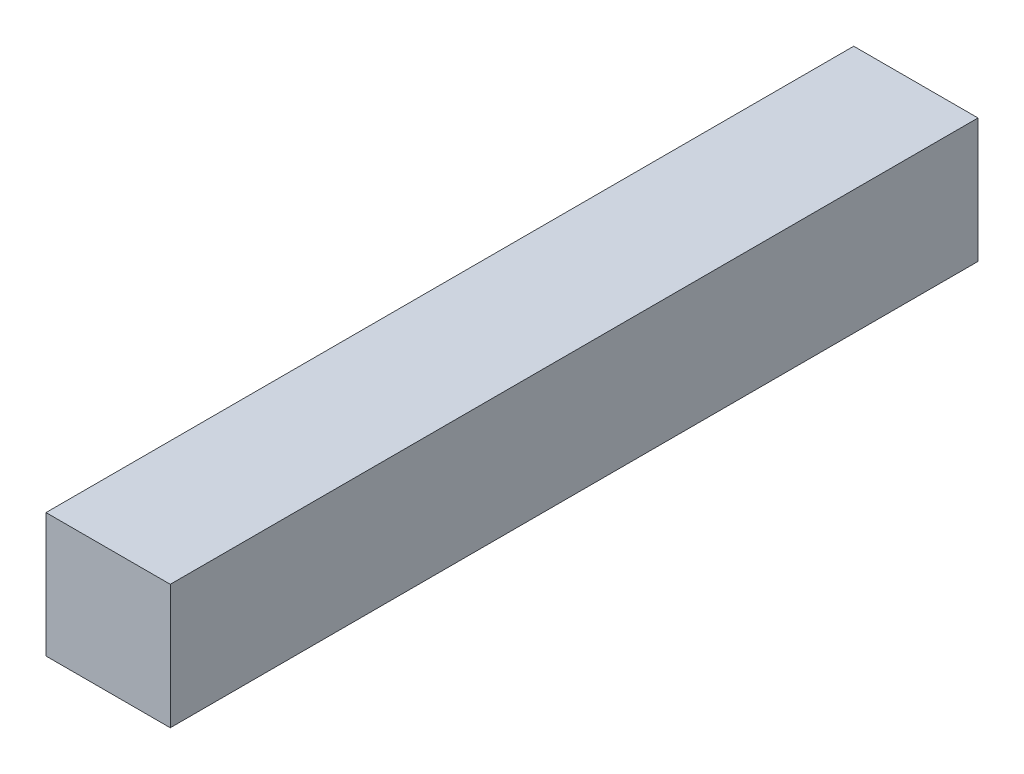
SolidWorks part; units mm, degrees
ref_plane "Front Plane" through (0, 0, 0) normal (0, 0, 1) x (1, 0, 0)
ref_plane "Top Plane" through (0, 0, 0) normal (0, 1, 0) x (1, 0, 0)
ref_plane "Right Plane" through (0, 0, 0) normal (1, 0, 0) x (0, 0, -1)
sketch "Sketch1" plane through (0, 0, 0) normal (0, 0, 1) x (1, 0, 0)
  line L1 (-7, -7) -> (7, -7)
  line L2 (-7, -7) -> (-7, 7)
  line L3 (-7, 7) -> (7, 7)
  line L4 (7, -7) -> (7, 7)
  line L5 (-7, -7) -> (7, 7) construction
  line L6 (-7, 7) -> (7, -7) construction
  point P0 (0, 0)
  dimension "D1" = 14
  dimension "D2" = 14
extrude "Boss-Extrude1" add sketch "Sketch1" along normal blind 91
